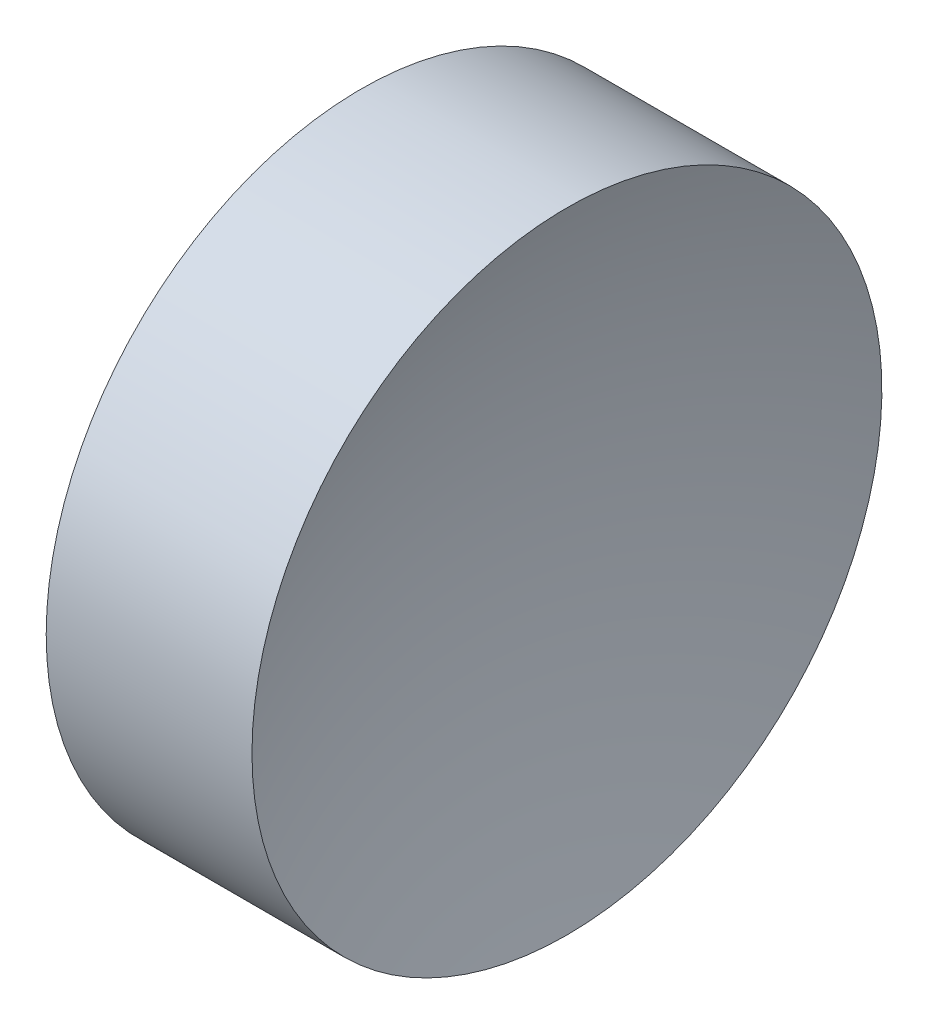
SolidWorks part; units mm, degrees
ref_plane "前视基准面" through (0, 0, 0) normal (0, 0, 1) x (1, 0, 0)
ref_plane "上视基准面" through (0, 0, 0) normal (0, 1, 0) x (1, 0, 0)
ref_plane "右视基准面" through (0, 0, 0) normal (1, 0, 0) x (0, 0, -1)
sketch "草图2" plane through (0, 0, 0) normal (0, 0, 1) x (1, 0, 0)
  line L0 (21.1565, 13.0311) -> (26.8361, 13.0311) construction
  line L1 (22.2009, 13.0311) -> (22.2009, 16.1811)
  line L2 (22.2009, 16.1811) -> (24.2589, 16.1811)
  line L3 (23.7009, 13.0311) -> (22.2009, 13.0311)
  arc A0 (24.2589, 16.1811) -> (23.7009, 13.0311) centre (32.8709, 13.0311) ccw
revolve "旋转1" add sketch "草图2" angle 360 about L0
